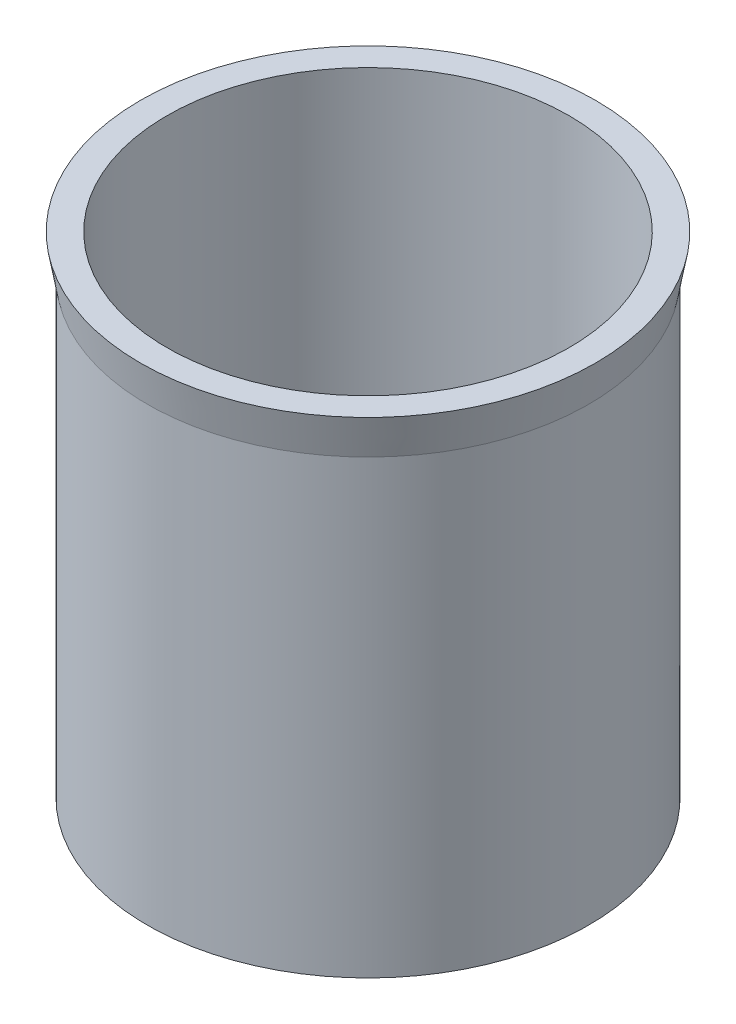
SolidWorks part; units mm, degrees
ref_plane "Front Plane" through (0, 0, 0) normal (0, 0, 1) x (1, 0, 0)
ref_plane "Top Plane" through (0, 0, 0) normal (0, 1, 0) x (1, 0, 0)
ref_plane "Right Plane" through (0, 0, 0) normal (1, 0, 0) x (0, 0, -1)
sketch "Sketch1" plane through (0, 0, 0) normal (0, 0, 1) x (1, 0, 0)
  line L0 (41, 0) -> (45, 0)
  line L1 (45, -8) -> (45, -100)
  line L2 (45, -100) -> (43.6449, -100)
  line L3 (41, -85) -> (41, 0)
  line L4 (0, 0) -> (0, 46.1813) construction
  line L5 (45, -8) -> (46.4106, 0)
  line L6 (46.4106, 0) -> (45, 0)
  line L7 (45, 0) -> (45, -8) construction
  line L8 (43.6449, -100) -> (41, -85)
  dimension "D1" = 82
  dimension "D2" = 100
  dimension "D3" = 4
  dimension "D4" = 10
  dimension "D5" = 8
  dimension "D6" = 10
  dimension "D7" = 15
revolve "Revolve1" add sketch "Sketch1" angle 360 about L4
